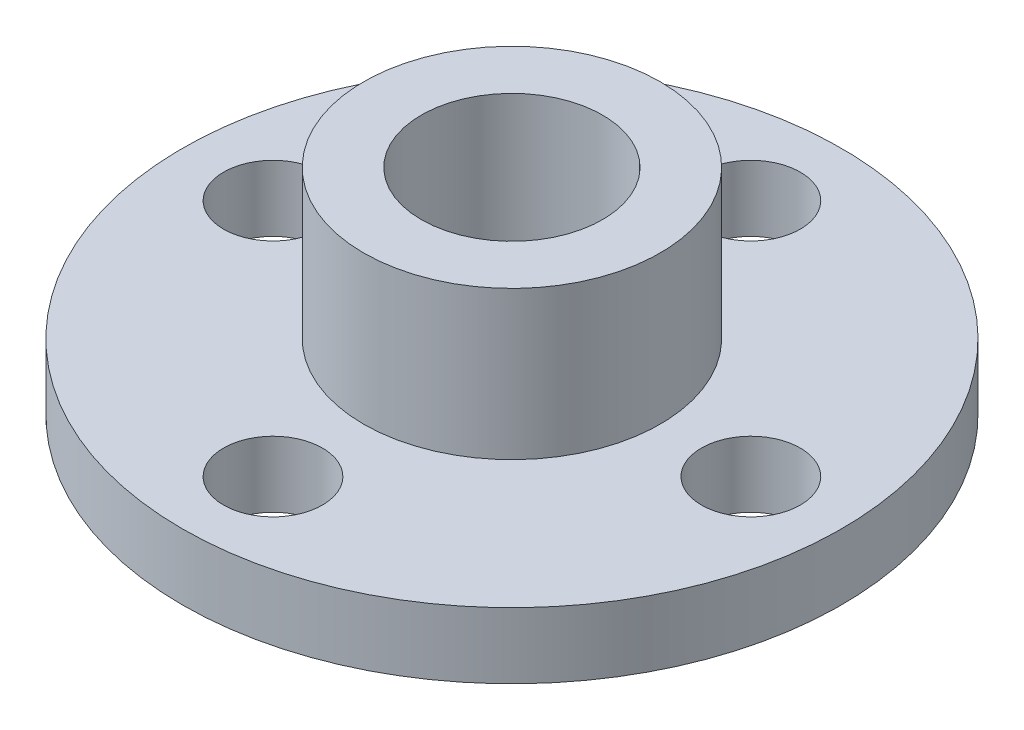
SolidWorks part; units mm, degrees
ref_plane "Front Plane" through (0, 0, 0) normal (0, 0, 1) x (1, 0, 0)
ref_plane "Top Plane" through (0, 0, 0) normal (0, 1, 0) x (1, 0, 0)
ref_plane "Right Plane" through (0, 0, 0) normal (1, 0, 0) x (0, 0, -1)
sketch "Sketch1" plane through (0, 0, 0) normal (0, 1, 0) x (1, 0, 0)
  line L0 (-10, 0) -> (-4.5, 0) construction
  circle A0 centre (0, 0) radius 10
  circle A4 centre (-7.25, 0) radius 1.5
  circle A5 centre (0, 0) radius 4.5
  circle A6 centre (0, 7.25) radius 1.5
  circle A7 centre (7.25, 0) radius 1.5
  circle A8 centre (0, -7.25) radius 1.5
  circle A9 centre (0, 0) radius 2
  point P16 (0, 0)
  dimension "D1" = 20
  dimension "D2" = 3
  dimension "D3" = 9
  dimension "D5" = 4
  dimension "D4" = 4
  dimension "D6" = 7.25
extrude "Boss-Extrude1" add sketch "Sketch1" along normal blind 2 contours A4 L0 | L0 A4 | A8 | A7 | A6 | A9 | A0
sketch "Sketch2" plane through (0, 2, 0) normal (0, 1, 0) x (1, 0, 0)
  circle A0 centre (0, 0) radius 4.5
  circle A1 centre (0, 0) radius 2.75
  dimension "D1" = 5.5
  dimension "D2" = 9
extrude "Boss-Extrude2" add sketch "Sketch2" along normal blind 4.5
